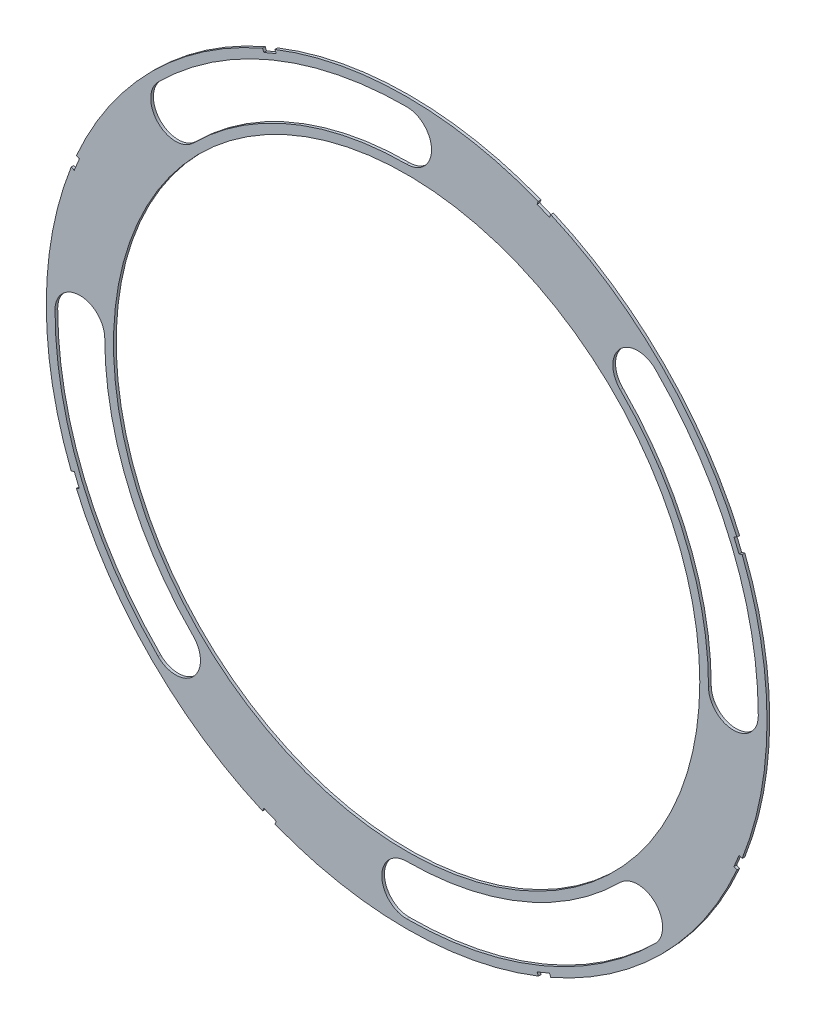
SolidWorks part; units mm, degrees
material "PTFE (general)"
ref_plane "Front Plane" through (0, 0, 0) normal (0, 0, 1) x (1, 0, 0)
ref_plane "Top Plane" through (0, 0, 0) normal (0, 1, 0) x (1, 0, 0)
ref_plane "Right Plane" through (0, 0, 0) normal (1, 0, 0) x (0, 0, -1)
sketch "Sketch4" plane through (0, 0, 0) normal (0, 0, 1) x (1, 0, 0)
  circle A0 centre (0, 0) radius 68.072
  dimension "D1" = 136.144
extrude "Boss-Extrude2" add sketch "Sketch4" along normal blind 0.508
sketch "Sketch5" plane through (0, 0, 0.508) normal (0, 0, 1) x (1, 0, 0)
  circle A0 centre (0, 0) radius 55.372
  circle A1 centre (0, 0) radius 68.072 construction
  dimension "D1" = 12.7
extrude "Cut-Extrude5" cut sketch "Sketch5" against normal through all
sketch "Sketch6" plane through (0, 0, 0.508) normal (0, 0, 1) x (1, 0, 0)
  line L0 (0, 0) -> (36.195, 0) construction
  line L1 (0, 0) -> (48.1342, -48.1342) construction
  line L2 (0, 0) -> (0, -68.072) construction
  line L3 (0, 0) -> (0, -68.072) construction
  line L4 (0, 0) -> (48.1342, -48.1342) construction
  line L5 (0, 0) -> (-48.1342, -48.1342) construction
  line L6 (0, 0) -> (-48.1342, -48.1342) construction
  line L7 (0, 0) -> (-68.072, 0) construction
  line L8 (0, 0) -> (-68.072, 0) construction
  line L9 (0, 0) -> (-48.1342, 48.1342) construction
  line L10 (0, 0) -> (-48.1342, 48.1342) construction
  line L11 (0, 0) -> (0, 68.072) construction
  line L12 (0, 0) -> (0, 68.072) construction
  line L13 (0, 0) -> (40.3213, -40.3214) construction
  line L14 (0, 0) -> (-40.3214, -40.3213) construction
  line L15 (0, 0) -> (48.1342, 48.1342) construction
  line L16 (0, 0) -> (48.1342, 48.1342) construction
  line L17 (0, 0) -> (68.072, 0) construction
  line L18 (0, 0) -> (68.072, 0) construction
  arc A0 (46.9667, 46.9667) -> (40.3214, 40.3213) centre (43.644, 43.644) ccw
  circle A1 centre (0, 0) radius 68.072 construction
  arc A2 (46.9667, -46.9667) -> (40.3213, -40.3214) centre (43.644, -43.644) ccw
  arc A3 (40.3213, -40.3214) -> (0, -57.023) centre (0, 0) cw
  arc A4 (0, -57.023) -> (0, -66.421) centre (0, -61.722) ccw
  arc A5 (0, -66.421) -> (46.9667, -46.9667) centre (0, 0) ccw
  arc A6 (-46.9667, -46.9667) -> (-40.3214, -40.3213) centre (-43.644, -43.644) ccw
  arc A7 (-40.3214, -40.3213) -> (-57.023, 0) centre (0, 0) cw
  arc A8 (-66.421, 0) -> (-46.9667, -46.9667) centre (0, 0) ccw
  arc A9 (-57.023, 0) -> (-66.421, 0) centre (-61.722, 0) ccw
  arc A10 (-46.9667, 46.9667) -> (-40.3213, 40.3214) centre (-43.644, 43.644) ccw
  arc A11 (-40.3213, 40.3214) -> (0, 57.023) centre (0, 0) cw
  arc A12 (0, 66.421) -> (-46.9667, 46.9667) centre (0, 0) ccw
  arc A13 (0, 57.023) -> (0, 66.421) centre (0, 61.722) ccw
  arc A14 (40.3214, 40.3213) -> (57.023, 0) centre (0, 0) cw
  arc A15 (66.421, 0) -> (46.9667, 46.9667) centre (0, 0) ccw
  circle A16 centre (0, 0) radius 55.372 construction
  arc A17 (57.023, 0) -> (66.421, 0) centre (61.722, 0) ccw
  point P4 (43.644, -43.644)
  point P11 (0, -61.722)
  point P13 (-43.644, -43.644)
  point P22 (43.644, 43.644)
  point P27 (-61.722, 0)
  point P30 (0, 0)
  point P36 (-43.644, 43.644)
  point P41 (0, 61.722)
  point P55 (61.722, 0)
  dimension "D2" = 4
  dimension "D3" = 45
  dimension "D4" = 90
  dimension "D6" = 6.35
  dimension "D7" = 9.398
  dimension "D8" = 4.699
  dimension "D9" = 4.699
  dimension "D5" = 6.35
  dimension "D10" = 90
extrude "Cut-Extrude6" cut sketch "Sketch6" against normal through all
sketch "Sketch8" plane through (0, 0, 0.508) normal (0, 0, 1) x (1, 0, 0)
  line L2 (63.963, 25.1197) -> (62.991, 27.4664)
  line L3 (63.963, 25.1197) -> (62.7897, 24.6337)
  line L4 (62.7897, 24.6337) -> (61.8177, 26.9803)
  line L5 (62.991, 27.4664) -> (61.8177, 26.9803)
  line L6 (0, 0) -> (68.072, 0) construction
  line L7 (-25.1197, 63.963) -> (-27.4664, 62.991)
  line L8 (-25.1197, 63.963) -> (-24.6337, 62.7897)
  line L9 (-27.4664, 62.991) -> (-26.9803, 61.8177)
  line L10 (-24.6337, 62.7897) -> (-26.9803, 61.8177)
  line L11 (-27.4664, 62.991) -> (-24.6337, 62.7897) construction
  line L12 (-25.1197, 63.963) -> (-26.9803, 61.8177) construction
  line L13 (-62.991, 27.4664) -> (-63.963, 25.1197)
  line L14 (-62.991, 27.4664) -> (-61.8177, 26.9803)
  line L15 (-61.8177, 26.9803) -> (-62.7897, 24.6337)
  line L16 (-63.963, 25.1197) -> (-62.7897, 24.6337)
  line L17 (-62.991, 27.4664) -> (-62.7897, 24.6337) construction
  line L18 (-63.963, 25.1197) -> (-61.8177, 26.9803) construction
  line L19 (-63.963, -25.1197) -> (-62.991, -27.4664)
  line L20 (-63.963, -25.1197) -> (-62.7897, -24.6337)
  line L21 (-62.7897, -24.6337) -> (-61.8177, -26.9803)
  line L22 (-62.991, -27.4664) -> (-61.8177, -26.9803)
  line L23 (-63.963, -25.1197) -> (-61.8177, -26.9803) construction
  line L24 (-62.991, -27.4664) -> (-62.7897, -24.6337) construction
  line L25 (-27.4664, -62.991) -> (-25.1197, -63.963)
  line L26 (-27.4664, -62.991) -> (-26.9803, -61.8177)
  line L27 (-26.9803, -61.8177) -> (-24.6337, -62.7897)
  line L28 (-25.1197, -63.963) -> (-24.6337, -62.7897)
  line L29 (-27.4664, -62.991) -> (-24.6337, -62.7897) construction
  line L30 (-25.1197, -63.963) -> (-26.9803, -61.8177) construction
  line L31 (25.1197, -63.963) -> (27.4664, -62.991)
  line L32 (25.1197, -63.963) -> (24.6337, -62.7897)
  line L33 (24.6337, -62.7897) -> (26.9803, -61.8177)
  line L34 (27.4664, -62.991) -> (26.9803, -61.8177)
  line L35 (25.1197, -63.963) -> (26.9803, -61.8177) construction
  line L36 (27.4664, -62.991) -> (24.6337, -62.7897) construction
  line L37 (62.991, -27.4664) -> (63.963, -25.1197)
  line L38 (62.991, -27.4664) -> (61.8177, -26.9803)
  line L39 (61.8177, -26.9803) -> (62.7897, -24.6337)
  line L40 (63.963, -25.1197) -> (62.7897, -24.6337)
  line L41 (62.991, -27.4664) -> (62.7897, -24.6337) construction
  line L42 (63.963, -25.1197) -> (61.8177, -26.9803) construction
  line L43 (63.963, 25.1197) -> (61.8177, 26.9803) construction
  line L44 (62.991, 27.4664) -> (62.7897, 24.6337) construction
  line L45 (27.4664, 62.991) -> (25.1197, 63.963)
  line L46 (27.4664, 62.991) -> (26.9803, 61.8177)
  line L47 (26.9803, 61.8177) -> (24.6337, 62.7897)
  line L48 (25.1197, 63.963) -> (24.6337, 62.7897)
  line L49 (27.4664, 62.991) -> (24.6337, 62.7897) construction
  line L50 (25.1197, 63.963) -> (26.9803, 61.8177) construction
  circle A0 centre (0, 0) radius 68.072 construction
  point P3 (-26.05, 62.8903)
  point P11 (-62.8903, 26.05)
  point P15 (62.8903, 26.05)
  point P20 (-62.8903, -26.05)
  point P25 (-26.05, -62.8903)
  point P26 (0, 0)
  point P31 (26.05, -62.8903)
  point P36 (62.8903, -26.05)
  point P45 (26.05, 62.8903)
  point P46 (0, 0)
  dimension "D3" = 0.635
  dimension "D5" = 1.27
  dimension "D6" = 2.54
  dimension "D7" = 1.27
  dimension "D9" = 0.635
  dimension "D10" = 112.5
  dimension "D14" = 0.635
  dimension "D21" = 22.5
  dimension "D11" = 8
extrude "Cut-Extrude11" cut sketch "Sketch8" against normal through all
